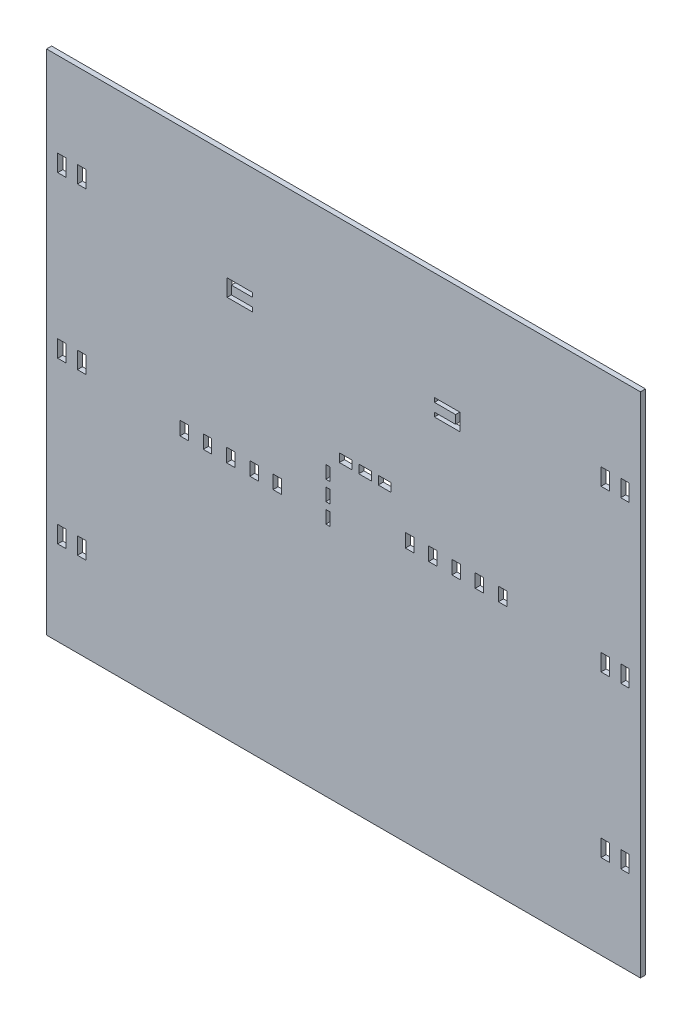
SolidWorks part; units mm, degrees
ref_plane "Front Plane" through (0, 0, 0) normal (0, 0, 1) x (1, 0, 0)
ref_plane "Top Plane" through (0, 0, 0) normal (0, 1, 0) x (1, 0, 0)
ref_plane "Right Plane" through (0, 0, 0) normal (1, 0, 0) x (0, 0, -1)
sketch "Sketch1" plane through (0, 0, 0) normal (0, 0, 1) x (1, 0, 0)
  line L0 (-351.1062, 300.025) -> (351.1062, -300.025) construction
  line L1 (-351.1062, -300.025) -> (351.1062, -300.025)
  line L2 (-351.1062, -300.025) -> (-351.1062, 300.025)
  line L3 (-351.1062, 300.025) -> (351.1062, 300.025)
  line L4 (351.1062, -300.025) -> (351.1062, 300.025)
  line L5 (351.1062, -300.025) -> (350.3687, -299.8406) construction
  line L6 (351.1062, 300.025) -> (0, 0) construction
  line L7 (0, 0) -> (-351.1062, -300.025) construction
  line L8 (291.1062, 300.025) -> (291.1062, -300.025) construction
  line L9 (0, 0) -> (291.1062, 0) construction
  line L10 (291.1062, 190.025) -> (304.4395, 190.025) construction
  line L11 (337.7728, 200.025) -> (327.7728, 200.025)
  line L12 (337.7728, 200.025) -> (337.7728, 180.025)
  line L13 (337.7728, 180.025) -> (327.7728, 180.025)
  line L14 (327.7728, 200.025) -> (327.7728, 180.025)
  line L15 (314.4395, 200.025) -> (304.4395, 200.025)
  line L16 (314.4395, 200.025) -> (314.4395, 180.025)
  line L17 (314.4395, 180.025) -> (304.4395, 180.025)
  line L18 (304.4395, 200.025) -> (304.4395, 180.025)
  line L19 (314.4395, 190.025) -> (327.7728, 190.025) construction
  line L20 (337.7728, 190.025) -> (351.1062, 190.025) construction
  line L21 (291.1062, 0) -> (304.4395, 0) construction
  line L22 (304.4395, 10) -> (314.4395, 10)
  line L23 (304.4395, 10) -> (304.4395, -10)
  line L24 (304.4395, -200.025) -> (304.4395, -180.025)
  line L25 (314.4395, -180.025) -> (304.4395, -180.025)
  line L26 (314.4395, -200.025) -> (304.4395, -200.025)
  line L27 (314.4395, -200.025) -> (314.4395, -180.025)
  line L28 (327.7728, -200.025) -> (327.7728, -180.025)
  line L29 (337.7728, -180.025) -> (327.7728, -180.025)
  line L30 (337.7728, -200.025) -> (337.7728, -180.025)
  line L31 (337.7728, -200.025) -> (327.7728, -200.025)
  line L32 (0, 300.025) -> (0, -300.025) construction
  line L33 (304.4395, -10) -> (314.4395, -10)
  line L34 (314.4395, 10) -> (314.4395, -10)
  line L35 (327.7728, 10) -> (337.7728, 10)
  line L36 (327.7728, 10) -> (327.7728, -10)
  line L37 (327.7728, -10) -> (337.7728, -10)
  line L38 (337.7728, 10) -> (337.7728, -10)
  line L39 (304.4395, 0) -> (314.4395, 0) construction
  line L40 (314.4395, 0) -> (327.7728, 0) construction
  line L41 (327.7728, 0) -> (337.7728, 0) construction
  line L42 (-337.7728, -200.025) -> (-327.7728, -200.025)
  line L43 (-337.7728, -200.025) -> (-337.7728, -180.025)
  line L44 (-337.7728, -180.025) -> (-327.7728, -180.025)
  line L45 (-327.7728, -200.025) -> (-327.7728, -180.025)
  line L46 (-314.4395, -200.025) -> (-314.4395, -180.025)
  line L47 (-314.4395, -200.025) -> (-304.4395, -200.025)
  line L48 (-314.4395, -180.025) -> (-304.4395, -180.025)
  line L49 (-98.4, 90) -> (98.4, -90) construction
  line L50 (98.4, 90) -> (0, 0) construction
  line L51 (0, 0) -> (-98.4, -90) construction
  line L52 (0.4925, 35.6474) -> (0.4925, -144.3526) construction
  line L53 (-15.85, 90) -> (-15.85, -90) construction
  line L54 (-20.85, 90) -> (-20.85, -90) construction
  line L55 (98.4, -6.3) -> (-98.4, -6.3) construction
  line L56 (-20.85, -90) -> (-20.85, -6.3) construction
  line L57 (-20.85, -6.3) -> (-15.85, -6.3) construction
  line L58 (-98.4, 49.7) -> (98.4, 49.7) construction
  line L59 (-20.85, -6.3) -> (-15.85, -6.3)
  line L60 (-20.85, -6.3) -> (-20.85, -21.3)
  line L61 (-20.85, -21.3) -> (-15.85, -21.3)
  line L62 (-15.85, -6.3) -> (-15.85, -21.3)
  line L63 (-20.85, 1.7) -> (-15.85, 1.7)
  line L64 (-20.85, 1.7) -> (-20.85, 16.7)
  line L65 (-20.85, 16.7) -> (-15.85, 16.7)
  line L66 (-15.85, 1.7) -> (-15.85, 16.7)
  line L67 (-20.85, 24.7) -> (-15.85, 24.7)
  line L68 (-20.85, 24.7) -> (-20.85, 39.7)
  line L69 (-20.85, 39.7) -> (-15.85, 39.7)
  line L70 (-15.85, 24.7) -> (-15.85, 39.7)
  line L71 (-98.4, 59.7) -> (98.4, 59.7) construction
  line L72 (-4.85, 90) -> (-4.85, -90) construction
  line L73 (-4.85, 90) -> (-4.85, 59.7) construction
  line L74 (-4.85, 59.7) -> (-4.85, 49.7) construction
  line L75 (-4.85, 59.7) -> (10.15, 59.7)
  line L76 (-4.85, 59.7) -> (-4.85, 49.7)
  line L77 (-4.85, 49.7) -> (10.15, 49.7)
  line L78 (10.15, 59.7) -> (10.15, 49.7)
  line L79 (18.15, 49.7) -> (33.15, 49.7)
  line L80 (18.15, 49.7) -> (18.15, 59.7)
  line L81 (18.15, 59.7) -> (33.15, 59.7)
  line L82 (33.15, 49.7) -> (33.15, 59.7)
  line L83 (41.15, 49.7) -> (56.15, 49.7)
  line L84 (41.15, 49.7) -> (41.15, 59.7)
  line L85 (41.15, 59.7) -> (56.15, 59.7)
  line L86 (56.15, 49.7) -> (56.15, 59.7)
  line L87 (-132.5, 155) -> (-107.5, 155) construction
  line L88 (-132.5, 157.5) -> (-107.5, 157.5)
  line L89 (-132.5, 157.5) -> (-132.5, 152.5)
  line L90 (-132.5, 152.5) -> (-107.5, 152.5)
  line L91 (-107.5, 157.5) -> (-107.5, 152.5)
  line L92 (-137.5, 172.5) -> (-132.5, 172.5)
  line L93 (-137.5, 172.5) -> (-137.5, 152.5)
  line L94 (-137.5, 152.5) -> (-132.5, 152.5)
  line L95 (-132.5, 172.5) -> (-132.5, 152.5)
  line L96 (-137.5, 162.5) -> (-132.5, 162.5) construction
  line L97 (-132.5, 167.5) -> (-132.5, 157.5) construction
  line L98 (-132.5, 162.5) -> (-107.5, 162.5) construction
  line L99 (-132.5, 172.5) -> (-107.5, 172.5)
  line L100 (-132.5, 172.5) -> (-132.5, 167.5)
  line L101 (-132.5, 167.5) -> (-107.5, 167.5)
  line L102 (-107.5, 172.5) -> (-107.5, 167.5)
  line L103 (-107.5, 162.5) -> (-107.5, 157.5) construction
  line L104 (107.5, 162.5) -> (107.5, 157.5) construction
  line L105 (132.5, 162.5) -> (107.5, 162.5) construction
  line L106 (132.5, 167.5) -> (132.5, 157.5) construction
  line L107 (137.5, 162.5) -> (132.5, 162.5) construction
  line L108 (132.5, 155) -> (107.5, 155) construction
  line L109 (107.5, 172.5) -> (107.5, 167.5)
  line L110 (132.5, 167.5) -> (107.5, 167.5)
  line L111 (132.5, 172.5) -> (132.5, 167.5)
  line L112 (132.5, 172.5) -> (107.5, 172.5)
  line L113 (137.5, 152.5) -> (132.5, 152.5)
  line L114 (137.5, 172.5) -> (137.5, 152.5)
  line L115 (137.5, 172.5) -> (132.5, 172.5)
  line L116 (107.5, 157.5) -> (107.5, 152.5)
  line L117 (132.5, 152.5) -> (107.5, 152.5)
  line L118 (132.5, 157.5) -> (132.5, 152.5)
  line L119 (132.5, 157.5) -> (107.5, 157.5)
  line L120 (132.5, 167.5) -> (132.5, 157.5)
  line L121 (-304.4395, -200.025) -> (-304.4395, -180.025)
  line L122 (-337.7728, 10) -> (-337.7728, -10)
  line L123 (-327.7728, -10) -> (-337.7728, -10)
  line L124 (-327.7728, 10) -> (-327.7728, -10)
  line L125 (-327.7728, 10) -> (-337.7728, 10)
  line L126 (-314.4395, 10) -> (-314.4395, -10)
  line L127 (-304.4395, -10) -> (-314.4395, -10)
  line L128 (-304.4395, 10) -> (-304.4395, -10)
  line L129 (-304.4395, 10) -> (-314.4395, 10)
  line L130 (-193.2006, -300.025) -> (-193.2006, -19.2) construction
  line L131 (-304.4395, 200.025) -> (-304.4395, 180.025)
  line L132 (-314.4395, 180.025) -> (-304.4395, 180.025)
  line L133 (-314.4395, 200.025) -> (-314.4395, 180.025)
  line L134 (-314.4395, 200.025) -> (-304.4395, 200.025)
  line L135 (-327.7728, 200.025) -> (-327.7728, 180.025)
  line L136 (-337.7728, 180.025) -> (-327.7728, 180.025)
  line L137 (-337.7728, 200.025) -> (-337.7728, 180.025)
  line L138 (-337.7728, 200.025) -> (-327.7728, 200.025)
  line L139 (337.7728, 0) -> (351.1062, 0) construction
  line L140 (-351.1062, -19.2) -> (-193.2006, -19.2) construction
  line L141 (-193.2006, -1.2) -> (-193.2006, -9.2)
  line L142 (-193.2006, -9.2) -> (-193.2006, -17.2)
  line L143 (-183.2006, -17.2) -> (-183.2006, -9.2)
  line L144 (-183.2006, -9.2) -> (-183.2006, -1.2)
  line L145 (-183.2006, -1.2) -> (-193.2006, -1.2)
  line L146 (-193.2006, -17.2) -> (-183.2006, -17.2)
  line L147 (-155.7006, -9.2) -> (-155.7006, -1.2)
  line L148 (-155.7006, -1.2) -> (-165.7006, -1.2)
  line L149 (-165.7006, -1.2) -> (-165.7006, -9.2)
  line L150 (-165.7006, -9.2) -> (-165.7006, -17.2)
  line L151 (-165.7006, -17.2) -> (-155.7006, -17.2)
  line L152 (-155.7006, -17.2) -> (-155.7006, -9.2)
  line L153 (-128.2006, -9.2) -> (-128.2006, -1.2)
  line L154 (-128.2006, -1.2) -> (-138.2006, -1.2)
  line L155 (-138.2006, -1.2) -> (-138.2006, -9.2)
  line L156 (-138.2006, -9.2) -> (-138.2006, -17.2)
  line L157 (-138.2006, -17.2) -> (-128.2006, -17.2)
  line L158 (-128.2006, -17.2) -> (-128.2006, -9.2)
  line L159 (-100.7006, -9.2) -> (-100.7006, -1.2)
  line L160 (-100.7006, -1.2) -> (-110.7006, -1.2)
  line L161 (193.2005, 9.2) -> (193.2005, 17.2)
  line L162 (193.2005, 17.2) -> (183.2005, 17.2)
  line L163 (183.2005, 17.2) -> (183.2005, 9.2)
  line L164 (183.2005, 9.2) -> (183.2005, 1.2)
  line L165 (183.2005, 1.2) -> (193.2005, 1.2)
  line L166 (193.2005, 1.2) -> (193.2005, 9.2)
  line L167 (165.7005, 9.2) -> (165.7005, 17.2)
  line L168 (165.7005, 17.2) -> (155.7005, 17.2)
  line L169 (155.7005, 17.2) -> (155.7005, 9.2)
  line L170 (155.7005, 9.2) -> (155.7005, 1.2)
  line L171 (165.7005, 1.2) -> (165.7005, 9.2)
  line L172 (155.7005, 1.2) -> (165.7005, 1.2)
  line L173 (138.2005, 9.2) -> (138.2005, 17.2)
  line L174 (138.2005, 17.2) -> (128.2005, 17.2)
  line L175 (128.2005, 17.2) -> (128.2005, 9.2)
  line L176 (128.2005, 9.2) -> (128.2005, 1.2)
  line L177 (138.2005, 1.2) -> (138.2005, 9.2)
  line L178 (128.2005, 1.2) -> (138.2005, 1.2)
  line L179 (110.7005, 9.2) -> (110.7005, 17.2)
  line L180 (110.7005, 17.2) -> (100.7005, 17.2)
  line L181 (-183.2006, -9.2) -> (-193.2006, -9.2) construction
  line L182 (-193.2006, -9.2) -> (-351.1062, -9.2) construction
  line L183 (-110.7006, -1.2) -> (-110.7006, -9.2)
  line L184 (-110.7006, -9.2) -> (-110.7006, -17.2)
  line L185 (351.0062, 300.025) -> (351.0062, -300.025)
  line L186 (-351.0062, 300.025) -> (-351.0062, -300.025)
  line L187 (-110.7006, -17.2) -> (-100.7006, -17.2)
  line L188 (-100.7006, -17.2) -> (-100.7006, -9.2)
  line L189 (-73.2006, -9.2) -> (-73.2006, -1.2)
  line L190 (-73.2006, -1.2) -> (-83.2006, -1.2)
  line L191 (-83.2006, -1.2) -> (-83.2006, -9.2)
  line L192 (-83.2006, -9.2) -> (-83.2006, -17.2)
  line L193 (-83.2006, -17.2) -> (-73.2006, -17.2)
  line L194 (-73.2006, -17.2) -> (-73.2006, -9.2)
  line L195 (183.2005, 9.2) -> (193.2005, 9.2) construction
  line L196 (193.2005, 9.2) -> (351.1062, 9.2) construction
  line L197 (183.2005, -0.8) -> (193.2005, -0.8) construction
  line L198 (183.2005, -0.8) -> (193.2005, -0.8) construction
  line L199 (193.2005, -0.8) -> (351.1062, -0.8) construction
  line L200 (100.7005, 17.2) -> (100.7005, 9.2)
  line L201 (100.7005, 9.2) -> (100.7005, 1.2)
  line L202 (110.7005, 1.2) -> (110.7005, 9.2)
  line L203 (100.7005, 1.2) -> (110.7005, 1.2)
  line L204 (83.2005, 9.2) -> (83.2005, 17.2)
  line L205 (83.2005, 17.2) -> (73.2005, 17.2)
  line L206 (73.2005, 17.2) -> (73.2005, 9.2)
  line L207 (73.2005, 9.2) -> (73.2005, 1.2)
  line L208 (83.2005, 1.2) -> (83.2005, 9.2)
  line L209 (73.2005, 1.2) -> (83.2005, 1.2)
  dimension "D7" = 280.825
  dimension "D1" = 702.2124
  dimension "D2" = 600.05
  dimension "D3" = 60
  dimension "D4" = 20
  dimension "D5" = 10
  dimension "D6" = 100
  dimension "D8" = 6.3
  dimension "D9" = 15
  dimension "D10" = 8
  dimension "D11" = 8
  dimension "D12" = 49.7
  dimension "D13" = 8
  dimension "D14" = 8
  dimension "D15" = 15
  dimension "D16" = 157.9056
  dimension "D17" = 5
  dimension "D18" = 20
  dimension "D19" = 5
  dimension "D20" = 132.5
  dimension "D21" = 155
  dimension "D22" = 25
  dimension "D23" = 5
  dimension "D24" = 10
  dimension "D25" = 8
  dimension "D26" = 5
  dimension "D27" = 8
  dimension "D28" = 0.1
  dimension "D29" = 5
extrude "Boss-Extrude2" add sketch "Sketch1" along normal blind 6
